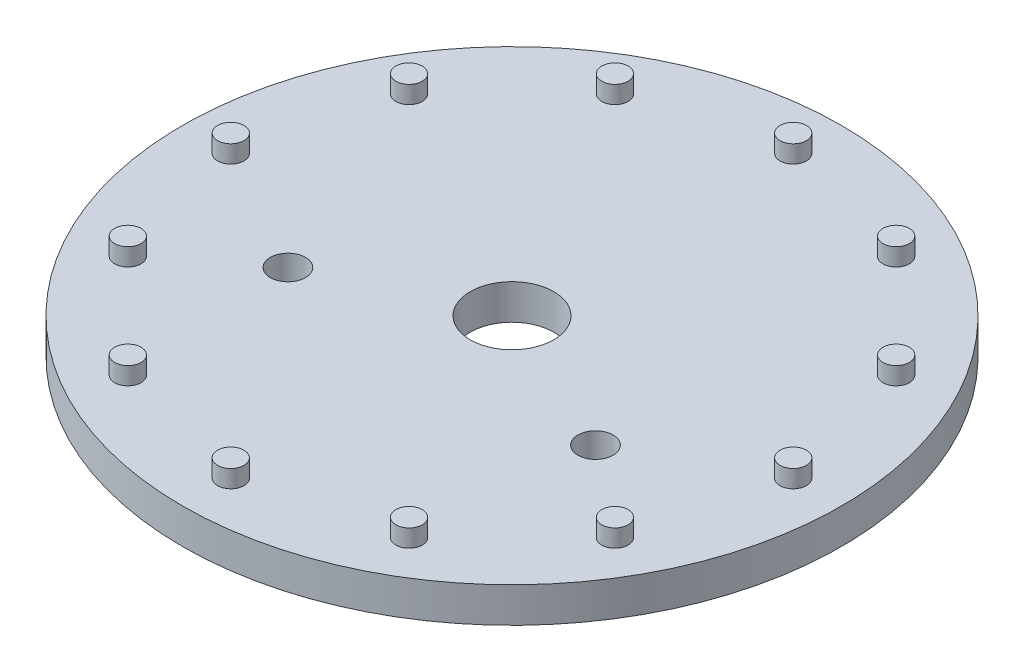
SolidWorks part; units mm, degrees
ref_plane "Front Plane" through (0, 0, 0) normal (0, 0, 1) x (1, 0, 0)
ref_plane "Top Plane" through (0, 0, 0) normal (0, 1, 0) x (1, 0, 0)
ref_plane "Right Plane" through (0, 0, 0) normal (1, 0, 0) x (0, 0, -1)
sketch "Sketch1" plane through (0, 0, 0) normal (0, 1, 0) x (1, 0, 0)
  circle A0 centre (0, 0) radius 37.5
  dimension "D1" = 75
extrude "Boss-Extrude1" add sketch "Sketch1" along normal blind 4
sketch "Sketch4" plane through (0, 4, 0) normal (0, 1, 0) x (1, 0, 0)
  line L0 (0, 0) -> (0, 56.6259) construction
  circle A0 centre (0, 32) radius 1.5
  circle A1 centre (16, 27.7128) radius 1.5
  circle A2 centre (27.7128, 16) radius 1.5
  circle A3 centre (32, 0) radius 1.5
  circle A4 centre (27.7128, -16) radius 1.5
  circle A5 centre (16, -27.7128) radius 1.5
  circle A6 centre (0, -32) radius 1.5
  circle A7 centre (-16, -27.7128) radius 1.5
  circle A8 centre (-27.7128, -16) radius 1.5
  circle A9 centre (-32, 0) radius 1.5
  circle A10 centre (-27.7128, 16) radius 1.5
  circle A11 centre (-16, 27.7128) radius 1.5
  point P30 (0, 0)
  dimension "D1" = 3
  dimension "D3" = 32
  dimension "D2" = 12
extrude "Boss-Extrude2" add sketch "Sketch4" along normal blind 2
sketch "Sketch5" plane through (0, 4, 0) normal (0, 1, 0) x (1, 0, 0)
  circle A0 centre (-17.5, -8) radius 2
  circle A1 centre (17.5, -8) radius 2
  dimension "D2" = 4
  dimension "D1" = 8
  dimension "D3" = 35
  dimension "D4" = 17.5
extrude "Cut-Extrude2" cut sketch "Sketch5" against normal blind 10
sketch "Sketch6" plane through (0, 4, 0) normal (0, 1, 0) x (1, 0, 0)
  circle A0 centre (0, 0) radius 4.75
  dimension "D1" = 9.5
extrude "Cut-Extrude3" cut sketch "Sketch6" against normal blind 42
